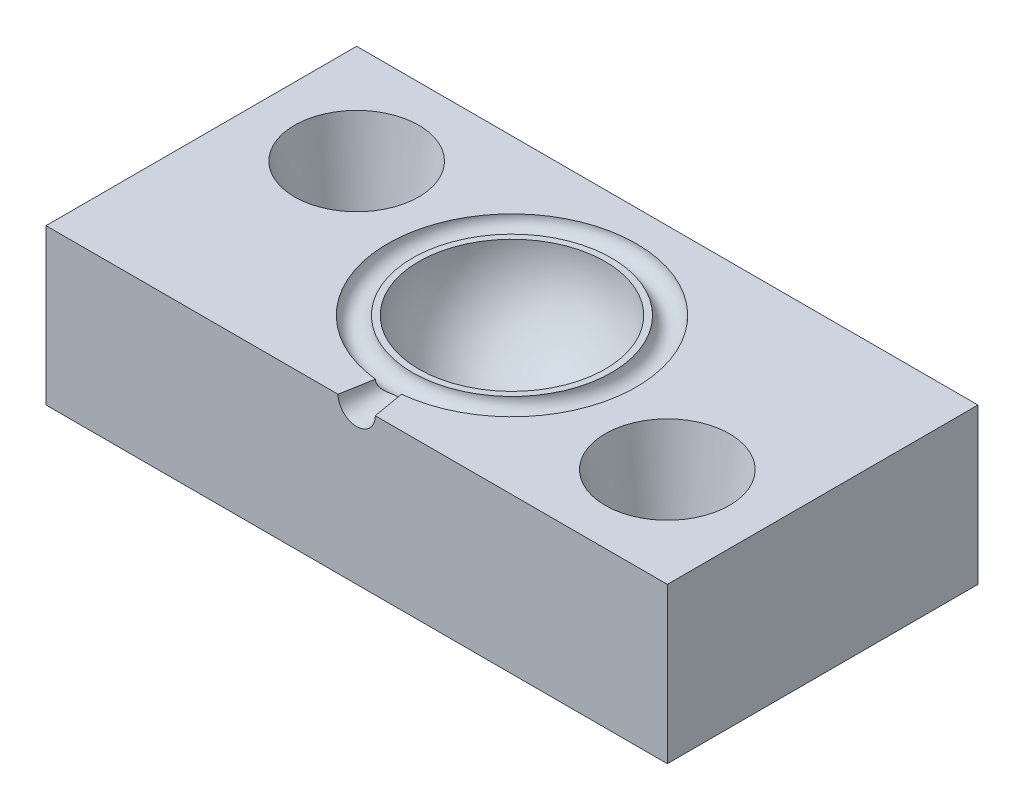
SolidWorks part; units mm, degrees
ref_plane "Plan de face" through (0, 0, 0) normal (0, 0, 1) x (1, 0, 0)
ref_plane "Plan de dessus" through (0, 0, 0) normal (0, 1, 0) x (1, 0, 0)
ref_plane "Plan de droite" through (0, 0, 0) normal (1, 0, 0) x (0, 0, -1)
sketch "Esquisse1" plane through (0, 0, 0) normal (0, 1, 0) x (1, 0, 0)
  line L1 (-25, 12.5) -> (25, 12.5)
  line L2 (-25, 12.5) -> (-25, -12.5)
  line L3 (-25, -12.5) -> (25, -12.5)
  line L4 (25, 12.5) -> (25, -12.5)
  dimension "D1" = 50
  dimension "D2" = 25
  dimension "D3" = 25
  dimension "D4" = 12.5
extrude "Boss.-Extru.1" add sketch "Esquisse1" along normal blind 12.5
sketch "Esquisse2" plane through (0, 12.5, 0) normal (0, 1, 0) x (1, 0, 0)
  line L0 (25, 12.5) -> (-25, 12.5) construction
  line L1 (-25, 12.5) -> (-25, -12.5) construction
  line L2 (25, -12.5) -> (25, 12.5) construction
  line L3 (-25, -12.5) -> (25, -12.5) construction
  circle A0 centre (17, -4.5) radius 5
  circle A1 centre (-17, 4.5) radius 5
  dimension "D1" = 10
  dimension "D2" = 10
  dimension "D3" = 8
  dimension "D4" = 8
  dimension "D5" = 8
  dimension "D6" = 8
extrude "Enlèv. mat.-Extru.1" cut sketch "Esquisse2" against normal through all draft 10
sketch "Esquisse3" plane through (0, 0, 0) normal (0, 0, 1) x (1, 0, 0)
  line L0 (-25, 12.5) -> (25, 12.5) construction
  line L1 (0, 20) -> (0, 5)
  arc A0 (0, 20) -> (0, 5) centre (0, 12.5) ccw
  point P5 (0, 12.5)
  dimension "D1" = 7.5
ref_axis "Axe1" through (0, 20, 0) along (0, -1, 0)
revolve "Enlèvement de matière-Révolution1" cut sketch "Esquisse3" angle 360 about axis through (0, 20, 0) along (0, -1, 0)
sketch "Esquisse4" plane through (0, 0, 0) normal (0, 0, 1) x (1, 0, 0)
  line L0 (-25, 12.5) -> (25, 12.5) construction
  line L1 (8, 12.5) -> (10, 12.5)
  arc A0 (10, 12.5) -> (8, 12.5) centre (9, 12.5) cw
  point P3 (0, 12.5)
  dimension "D1" = 1
  dimension "D2" = 9
revolve "Enlèvement de matière-Révolution3" cut sketch "Esquisse4" angle 360 about axis through (0, 20, 0) along (0, -1, 0)
shell "Coque1" thickness 3
sketch "Esquisse5" plane through (0, 0, 12.5) normal (0, 0, 1) x (1, 0, 0)
  line L0 (-25, 12.5) -> (25, 12.5) construction
  circle A0 centre (0, 12.5) radius 1.5
  dimension "D1" = 3
extrude "Enlèv. mat.-Extru.2" cut sketch "Esquisse5" against normal blind 4 draft 10
